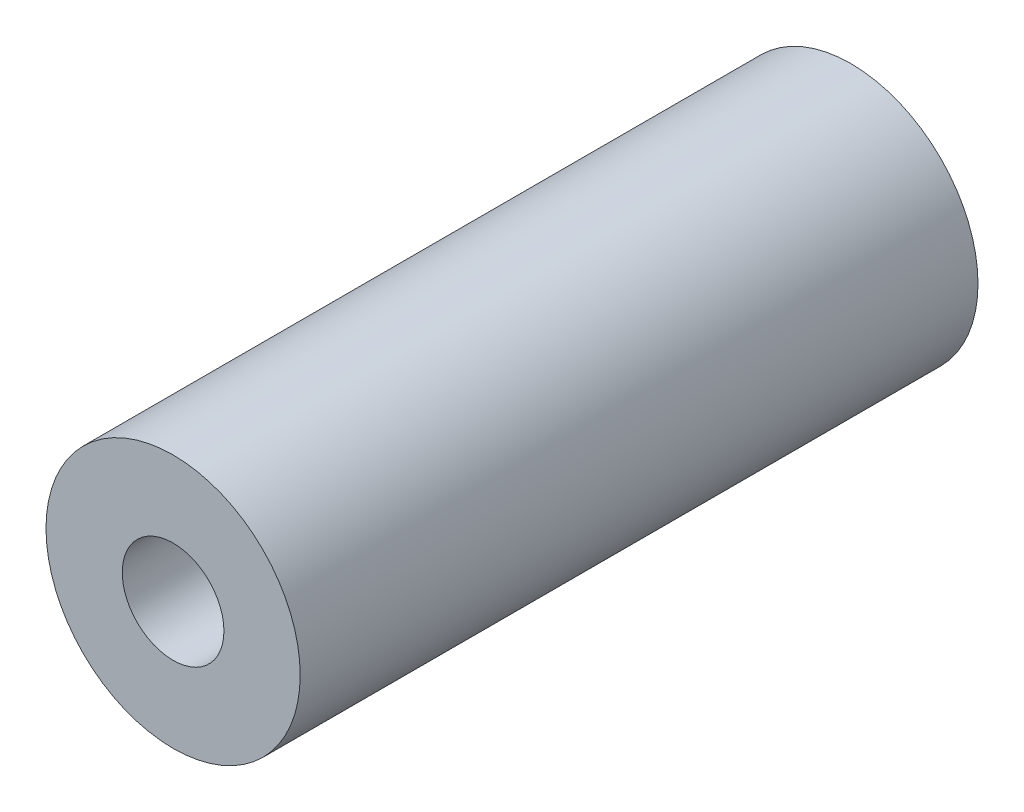
SolidWorks part; units mm, degrees
ref_plane "Front Plane" through (0, 0, 0) normal (0, 0, 1) x (1, 0, 0)
ref_plane "Top Plane" through (0, 0, 0) normal (0, 1, 0) x (1, 0, 0)
ref_plane "Right Plane" through (0, 0, 0) normal (1, 0, 0) x (0, 0, -1)
sketch "Sketch1" plane through (0, 0, 0) normal (0, 0, 1) x (1, 0, 0)
  circle A0 centre (0, 0) radius 7.5
  circle A1 centre (0, 0) radius 3
  dimension "D1" = 15
  dimension "D2" = 6
extrude "Boss-Extrude1" add sketch "Sketch1" along normal blind 40
